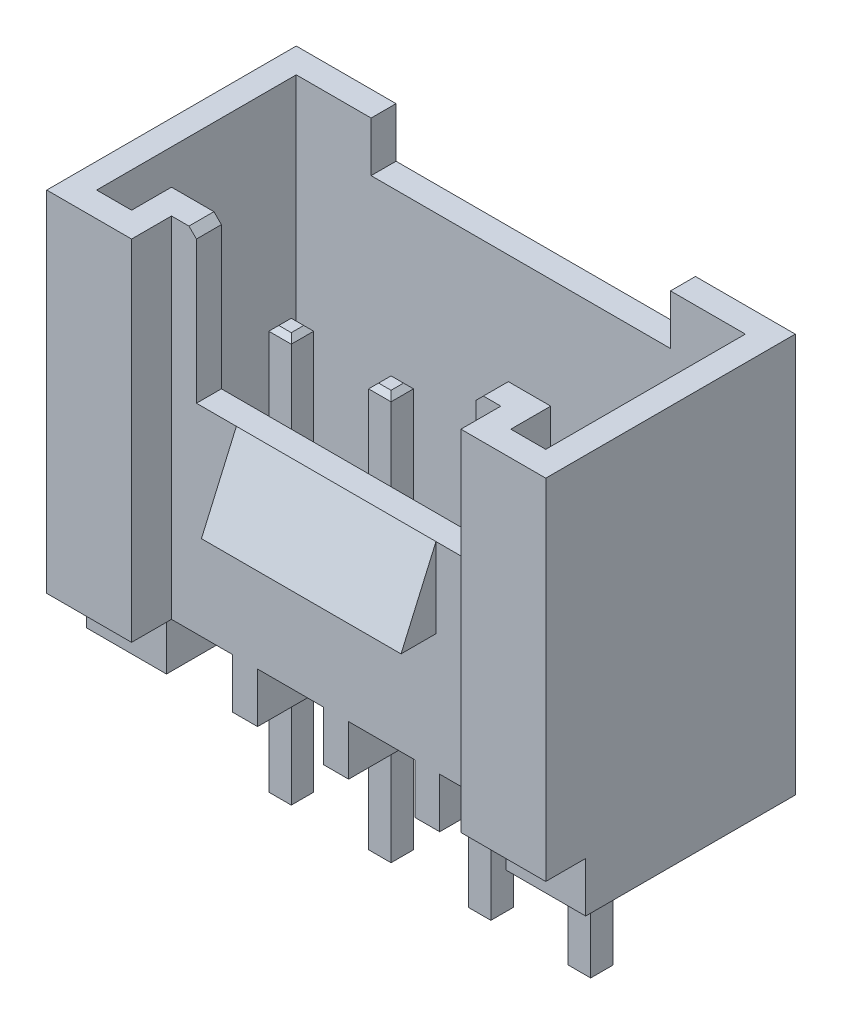
SolidWorks part; units mm, degrees
ref_plane "Plan de face" through (0, 0, 0) normal (0, 0, 1) x (1, 0, 0)
ref_plane "Plan de dessus" through (0, 0, 0) normal (0, 1, 0) x (1, 0, 0)
ref_plane "Plan de droite" through (0, 0, 0) normal (1, 0, 0) x (0, 0, -1)
sketch "Esquisse1" plane through (0, 0, 0) normal (0, 1, 0) x (1, 0, 0)
  line L1 (0, 0) -> (10, 0)
  line L2 (0, 0) -> (0, 5)
  line L3 (0, 5) -> (10, 5)
  line L4 (10, 0) -> (10, 5)
  dimension "D1" = 5
  dimension "D2" = 10
extrude "Boss.-Extru.1" add sketch "Esquisse1" along normal blind 8
sketch "Esquisse2" plane through (0, 8, 0) normal (0, 1, 0) x (1, 0, 0)
  line L0 (0, 0) -> (10, 0) construction
  line L1 (1.7, 0) -> (8.3, 0)
  line L2 (1.7, 0) -> (1.7, 0.8)
  line L3 (1.7, 0.8) -> (8.3, 0.8)
  line L4 (8.3, 0) -> (8.3, 0.8)
  line L5 (0, 5) -> (0, 0) construction
  line L6 (10, 0) -> (10, 5) construction
  dimension "D1" = 1.7
  dimension "D2" = 1.7
  dimension "D3" = 0.8
extrude "Enlèv. mat.-Extru.1" cut sketch "Esquisse2" against normal blind 8
sketch "Esquisse4" plane through (0, 8, 0) normal (0, 1, 0) x (1, 0, 0)
  line L16 (0.5, 0.5) -> (1.2, 0.5)
  line L17 (1.2, 0.5) -> (1.2, 1.3)
  line L18 (1.2, 1.3) -> (8.8, 1.3)
  line L19 (8.8, 1.3) -> (8.8, 0.5)
  line L20 (8.8, 0.5) -> (9.5, 0.5)
  line L21 (9.5, 0.5) -> (9.5, 4.5)
  line L22 (9.5, 4.5) -> (0.5, 4.5)
  line L23 (0.5, 4.5) -> (0.5, 0.5)
  line L24 (0.5, 0.5) -> (1.2, 0.5)
  line L25 (1.2, 0.5) -> (1.2, 1.3)
  line L26 (1.2, 1.3) -> (8.8, 1.3)
  line L27 (8.8, 1.3) -> (8.8, 0.5)
  line L28 (8.8, 0.5) -> (9.5, 0.5)
  line L29 (9.5, 0.5) -> (9.5, 4.5)
  line L30 (9.5, 4.5) -> (0.5, 4.5)
  line L31 (0.5, 4.5) -> (0.5, 0.5)
  dimension "D1" = 0.5
extrude "Enlèv. mat.-Extru.2" cut sketch "Esquisse4" against normal blind 6.5
sketch "Esquisse5" plane through (0, 8, 0) normal (0, 1, 0) x (1, 0, 0)
  line L0 (10, 5) -> (0, 5) construction
  line L1 (2, 5) -> (8, 5)
  line L2 (2, 5) -> (2, 4.5)
  line L3 (2, 4.5) -> (8, 4.5)
  line L4 (8, 5) -> (8, 4.5)
  line L5 (9.5, 4.5) -> (0.5, 4.5) construction
  line L6 (10, 0) -> (10, 5) construction
  line L7 (0, 5) -> (0, 0) construction
  dimension "D1" = 2
  dimension "D2" = 2
extrude "Enlèv. mat.-Extru.3" cut sketch "Esquisse5" against normal blind 1
sketch "Esquisse6" plane through (0, 8, 0) normal (0, 1, 0) x (1, 0, 0)
  line L0 (1.2, 1.3) -> (8.8, 1.3) construction
  line L1 (2.2, 1.3) -> (7.8, 1.3)
  line L2 (2.2, 1.3) -> (2.2, 0.8)
  line L3 (2.2, 0.8) -> (7.8, 0.8)
  line L4 (7.8, 1.3) -> (7.8, 0.8)
  line L5 (8.3, 0.8) -> (1.7, 0.8) construction
  line L6 (10, 0) -> (10, 5) construction
  line L7 (0, 5) -> (0, 0) construction
  dimension "D1" = 2.2
  dimension "D2" = 2.2
extrude "Enlèv. mat.-Extru.4" cut sketch "Esquisse6" against normal blind 3
sketch "Esquisse7" plane through (10, 0, 0) normal (1, 0, 0) x (0, 0, -1)
  line L1 (0, 0) -> (0.8, 0)
  line L2 (0, 0) -> (0, 1)
  line L3 (0, 1) -> (0.8, 1)
  line L4 (0.8, 0) -> (0.8, 1)
  dimension "D1" = 0.8
  dimension "D2" = 1
extrude "Enlèv. mat.-Extru.5" cut sketch "Esquisse7" against normal blind 10
sketch "Esquisse8" plane through (0, 0, 0) normal (0, -1, 0) x (1, 0, 0)
  line L0 (10, -0.8) -> (0, -0.8) construction
  line L1 (1.6, -0.8) -> (8.4, -0.8)
  line L2 (1.6, -0.8) -> (1.6, -5)
  line L3 (1.6, -5) -> (8.4, -5)
  line L4 (8.4, -0.8) -> (8.4, -5)
  line L5 (10, -5) -> (0, -5) construction
  line L6 (0, -5) -> (0, -0.8) construction
  line L7 (10, -0.8) -> (10, -5) construction
  dimension "D1" = 1.6
  dimension "D2" = 1.6
extrude "Enlèv. mat.-Extru.6" cut sketch "Esquisse8" against normal blind 1
sketch "Esquisse9" plane through (1.6, 0, 0) normal (1, 0, 0) x (0, 0, -1)
  line L0 (5, 1) -> (0.8, 1) construction
  line L1 (4.7, 1) -> (3.9, 0.2)
  line L2 (3.9, 0.2) -> (1.9, 0.2)
  line L3 (1.9, 0.2) -> (1.1, 1)
  line L4 (0.8, 0) -> (5, 0) construction
  line L5 (4.7, 1) -> (1.1, 1)
  dimension "D1" = 45
  dimension "D2" = 45
  dimension "D3" = 0.2
  dimension "D4" = 0.3
  dimension "D5" = 0.3
extrude "Boss.-Extru.2" add sketch "Esquisse9" along normal blind 6.8
ref_plane "Plan1" through (5, 0, 0) normal (1, 0, 0) x (0, 0, -1)
sketch "Esquisse11" plane through (5, 0, 0) normal (1, 0, 0) x (0, 0, -1)
  line L0 (0.8, 5) -> (0.1, 3.4)
  line L1 (0.1, 3.4) -> (0.8, 3.4)
  line L2 (0.8, 1) -> (0.8, 8) construction
  line L3 (0.8, 3.4) -> (0.8, 5)
  dimension "D1" = 1.6
  dimension "D2" = 0.7
extrude "Boss.-Extru.3" add sketch "Esquisse11" along normal blind 2 and the other way blind 2
ref_plane "Plan2" through (0, 1, 0) normal (0, 1, 0) x (1, 0, 0)
sketch "Esquisse12" plane through (0, 1, 0) normal (0, 1, 0) x (1, 0, 0)
  line L0 (8.3, 0.8) -> (1.7, 0.8) construction
  line L1 (1.6, 5) -> (8.4, 5) construction
  line L2 (3, 0.8) -> (7, 0.8) construction
  line L3 (4.75, 0.8) -> (5.25, 0.8)
  line L4 (4.75, 0.8) -> (4.75, 5)
  line L5 (4.75, 5) -> (5.25, 5)
  line L6 (5.25, 0.8) -> (5.25, 5)
  line L8 (2.925, 0.8) -> (3.425, 0.8)
  line L9 (2.925, 0.8) -> (2.925, 5)
  line L10 (2.925, 5) -> (3.425, 5)
  line L11 (3.425, 0.8) -> (3.425, 5)
  line L12 (6.575, 0.8) -> (7.075, 0.8)
  line L13 (6.575, 0.8) -> (6.575, 5)
  line L14 (6.575, 5) -> (7.075, 5)
  line L15 (7.075, 0.8) -> (7.075, 5)
  line L16 (3.175, 0.8) -> (3.175, 5) construction
  line L17 (6.825, 0.8) -> (6.825, 5) construction
  point P0 (5, 0.8)
  point P1 (5, 5)
  dimension "D1" = 0.5
  dimension "D2" = 0.25
  dimension "D3" = 0.5
  dimension "D4" = 0.5
  dimension "D5" = 0.25
  dimension "D6" = 0.25
  dimension "D7" = 1.575
  dimension "D8" = 1.575
extrude "Boss.-Extru.4" add sketch "Esquisse12" against normal blind 1
chamfer "Chanfrein1" distance 0.15 angle 45 2 edges at (2.2, 8, -1.05) (7.8, 8, -1.05)
sketch "Esquisse13" plane through (0, 0.2, 0) normal (0, -1, 0) x (1, 0, 0)
  line L0 (5, -0.8) -> (5, -5) construction
  line L1 (7.775, -2.675) -> (8.225, -2.675)
  line L2 (2.225, -2.675) -> (1.775, -2.675)
  line L3 (2.225, -2.675) -> (2.225, -3.125)
  line L4 (2.225, -3.125) -> (1.775, -3.125)
  line L5 (4.225, -3.125) -> (3.775, -3.125)
  line L6 (3.775, -2.675) -> (3.775, -3.125)
  line L7 (4.225, -2.675) -> (4.225, -3.125)
  line L8 (4.225, -2.675) -> (3.775, -2.675)
  line L9 (4.75, -0.8) -> (5.25, -0.8) construction
  line L10 (5.25, -5) -> (4.75, -5) construction
  line L11 (8.225, -2.675) -> (8.225, -3.125)
  line L12 (7.775, -3.125) -> (8.225, -3.125)
  line L13 (4.225, -2.9) -> (3.775, -2.9) construction
  line L14 (1.775, -2.675) -> (1.775, -3.125)
  line L15 (7.775, -2.675) -> (7.775, -3.125)
  line L19 (6.225, -2.675) -> (6.225, -3.125)
  line L20 (5.775, -3.125) -> (6.225, -3.125)
  line L21 (5.775, -2.675) -> (5.775, -3.125)
  line L22 (5.775, -2.675) -> (6.225, -2.675)
  line L27 (4.75, -1.9) -> (3.425, -1.9) construction
  dimension "D1" = 2
  dimension "D2" = 0.45
  dimension "D3" = 2
  dimension "D4" = 1
extrude "Boss.-Extru.5" add sketch "Esquisse13" along normal blind 3.2 and the other way blind 5
chamfer "Chanfrein2" distance 0.1 angle 45 32 edges at (2, -3, -3.125) (1.775, -3, -2.9) (2.225, -3, -2.9) (2, -3, -2.675) (4, -3, -3.125) (4.225, -3, -2.9) (4, -3, -2.675) (3.775, -3, -2.9) (5.775, -3, -2.9) (5.775, 5.2, -2.9) (4, 5.2, -2.675) (4.225, 5.2, -2.9) (4, 5.2, -3.125) (3.775, 5.2, -2.9) (2.225, 5.2, -2.9) (2, 5.2, -3.125) (1.775, 5.2, -2.9) (2, 5.2, -2.675) (8, 5.2, -3.125) (8.225, 5.2, -2.9) (8, 5.2, -2.675) (7.775, 5.2, -2.9) (6, 5.2, -3.125) (6.225, 5.2, -2.9) (6, 5.2, -2.675) (6.225, -3, -2.9) (6, -3, -3.125) (6, -3, -2.675) (8, -3, -2.675) (8.225, -3, -2.9) (8, -3, -3.125) (7.775, -3, -2.9)
